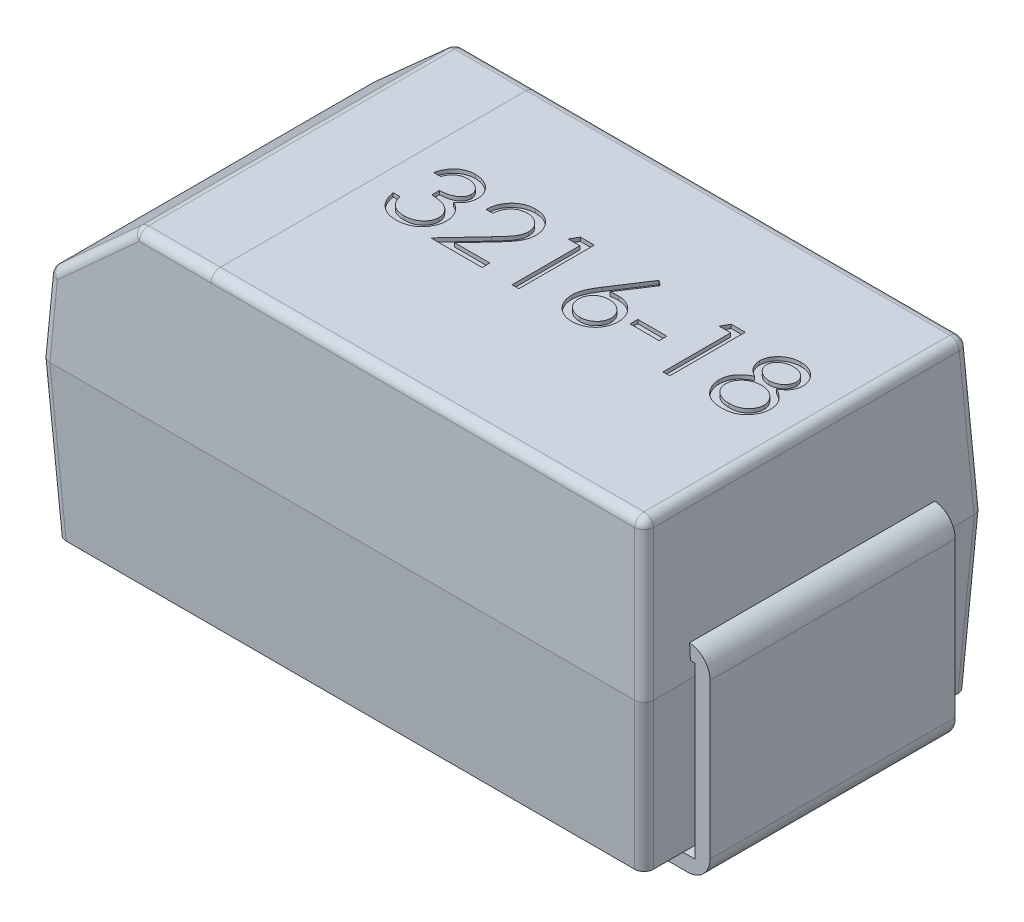
SolidWorks part; units mm, degrees
ref_plane "Front Plane" through (0, 0, 0) normal (0, 0, 1) x (1, 0, 0)
ref_plane "Top Plane" through (0, 0, 0) normal (0, 1, 0) x (1, 0, 0)
ref_plane "Right Plane" through (0, 0, 0) normal (1, 0, 0) x (0, 0, -1)
ref_plane "Plane1" through (0, 0.9, 0) normal (0, 1, 0) x (-1, 0, 0)
sketch "Sketch4" plane through (0, 0.9, 0) normal (0, 1, 0) x (-1, 0, 0)
  line L3 (1.6, -0.9) -> (-1.6, -0.9)
  line L4 (1.6, -0.9) -> (1.6, 0.9)
  line L5 (1.6, 0.9) -> (-1.6, 0.9)
  line L6 (-1.6, -0.9) -> (-1.6, 0.9)
  line L7 (1.6, -0.9) -> (-1.6, 0.9) construction
  line L8 (1.6, 0.9) -> (-1.6, -0.9) construction
  point P3 (-1.6, 0)
  point P5 (-1.6, 2.8231)
  point P6 (0, 0.9)
  point P7 (-4.8463, 0.9)
  point P12 (1.6, 0)
  dimension "D1" = 3.2
  dimension "D2" = 1.8
extrude "Boss-Extrude2" add sketch "Sketch4" against normal blind 0.82 draft 3 and the other way blind 0.8 draft 3
sketch "Sketch5" plane through (0, 0.08, 0) normal (0, -1, 0) x (1, 0, 0)
  line L0 (0.55, -0.65) -> (0.55, 0.65)
  line L1 (0, 0) -> (-0.55, 0) construction
  line L2 (0, 0) -> (0, 0.65) construction
  line L3 (0.55, 0.65) -> (-0.55, 0.65)
  line L4 (-0.55, -0.65) -> (-0.55, 0.65)
  line L5 (0.55, -0.65) -> (-0.55, -0.65)
  point P8 (0.55, 0)
  dimension "D1" = 0.65
  dimension "D2" = 0.55
extrude "Boss-Extrude3" add sketch "Sketch5" along normal blind 0.06
sketch "Sketch14" plane through (0, 0, 0) normal (0, 0, 1) x (1, 0, 0)
  line L0 (-0.9, 1.06) -> (-0.9, 0.98)
  line L1 (-0.9, 0.98) -> (-1.62, 0.98)
  line L2 (-1.62, 0.98) -> (-1.62, 0.08)
  line L3 (-1.62, 0.08) -> (-0.9, 0.08)
  line L4 (-0.9, 0.08) -> (-0.9, 0)
  line L5 (-0.9, 0) -> (-1.58, 0)
  line L6 (-1.7, 0.12) -> (-1.7, 0.94)
  line L7 (-1.58, 1.06) -> (-0.9, 1.06)
  line L8 (0, 0) -> (0, 1.6548) construction
  line L9 (1.58, 1.06) -> (0.9, 1.06)
  line L10 (1.7, 0.12) -> (1.7, 0.94)
  line L11 (0.9, 0) -> (1.58, 0)
  line L12 (0.9, 0.08) -> (0.9, 0)
  line L13 (1.62, 0.08) -> (0.9, 0.08)
  line L14 (1.62, 0.98) -> (1.62, 0.08)
  line L15 (0.9, 0.98) -> (1.62, 0.98)
  line L16 (0.9, 1.06) -> (0.9, 0.98)
  arc A0 (-1.58, 0) -> (-1.7, 0.12) centre (-1.58, 0.12) cw
  arc A1 (-1.7, 0.94) -> (-1.58, 1.06) centre (-1.58, 0.94) cw
  arc A2 (1.7, 0.94) -> (1.58, 1.06) centre (1.58, 0.94) ccw
  arc A3 (1.58, 0) -> (1.7, 0.12) centre (1.58, 0.12) ccw
  point P11 (-1.7, 0)
  point P14 (-1.7, 1.06)
  point P29 (1.7, 1.06)
  point P30 (1.7, 0)
  dimension "D6" = 0.12
  dimension "D1" = 0.8
  dimension "D2" = 0.08
  dimension "D3" = 1.06
  dimension "D4" = 0.9
  dimension "D5" = 0.08
extrude "Boss-Extrude7" add sketch "Sketch14" along normal mid plane 1.3 separate body
chamfer "Chamfer1" distance 0.4 angle 45 1 edges at (-1.5581, 1.7, 0)
sketch "Sketch15" plane through (0, 1.7, 0) normal (0, 1, 0) x (1, 0, 0)
  line L0 (-1.1354, -0.8581) -> (1.5581, -0.8581) construction
  line L1 (-1.1354, 0.8581) -> (-0.7354, 0.8581)
  line L2 (-1.1354, 0.8581) -> (-1.1354, -0.8581)
  line L3 (-1.1354, -0.8581) -> (-0.7354, -0.8581)
  line L4 (-0.7354, 0.8581) -> (-0.7354, -0.8581)
  dimension "D1" = 0.4
split line "Split Line1"
sketch "Sketch11" plane through (0, 1.7, 0) normal (0, 1, 0) x (1, 0, 0)
  line L0 (-0.7354, 0.8581) -> (-0.7354, -0.8581) construction
  line L1 (-0.7354, -0.8581) -> (1.5581, -0.8581) construction
  text T0 "3216-18" font "Century Gothic" height 0.4
  dimension "D1" = 0.1
  dimension "D2" = 0.74
extrude "Cut-Extrude2" cut sketch "Sketch11" against normal blind 0.02
fillet "Fillet6" radius 0.05 17 edges at (-1.5785, 0.49, 0.8785) (1.5785, 0.49, 0.8785) (1.5785, 0.49, -0.8785) (-1.5785, 0.49, -0.8785) (-0.9354, 1.7, -0.8581) (0.4114, 1.7, -0.8581) (-0.9354, 1.7, 0.8581) (-1.3572, 1.5003, -0.8685) (-1.5895, 1.1003, -0.8895) (-1.5895, 1.1003, 0.8895) (1.579, 1.3, 0.879) (1.579, 1.3, -0.879) (1.5581, 1.7, 0) (0.4114, 1.7, 0.8581) (-1.579, 1.3005, 0) (-1.1354, 1.7, 0) (-1.3572, 1.5003, 0.8685)
